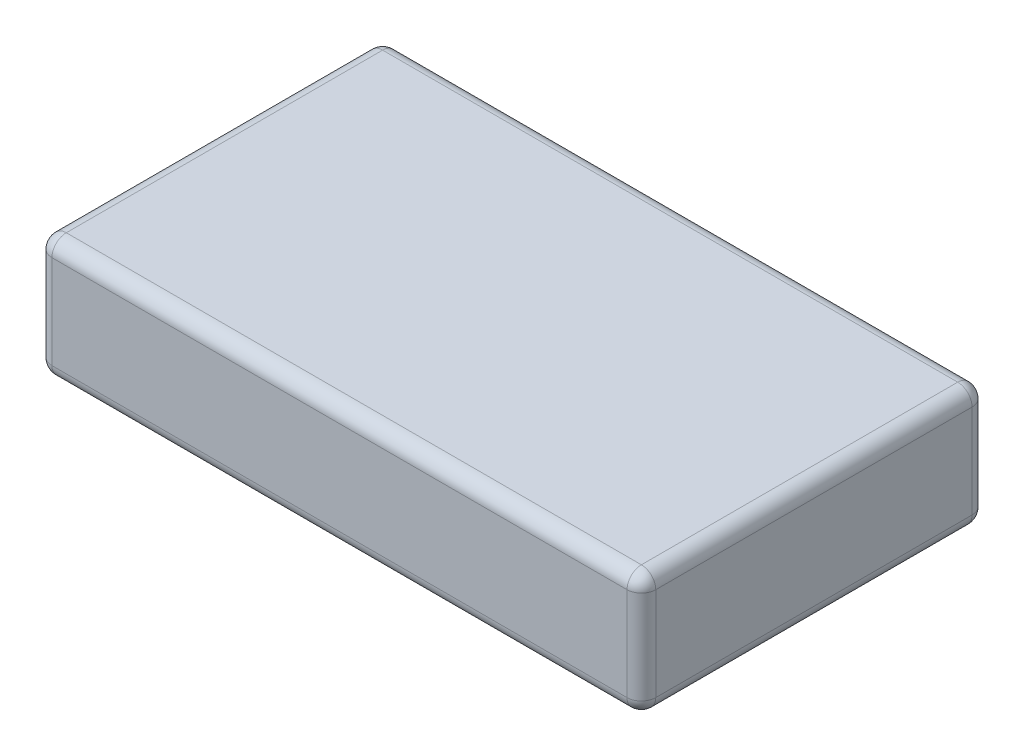
SolidWorks part; units mm, degrees
ref_plane "Front Plane" through (0, 0, 0) normal (0, 0, 1) x (1, 0, 0)
ref_plane "Top Plane" through (0, 0, 0) normal (0, 1, 0) x (1, 0, 0)
ref_plane "Right Plane" through (0, 0, 0) normal (1, 0, 0) x (0, 0, -1)
sketch "Sketch1" plane through (0, 0, 0) normal (0, 1, 0) x (1, 0, 0)
  line L1 (21, 12) -> (-21, 12)
  line L2 (21, 12) -> (21, -12)
  line L3 (21, -12) -> (-21, -12)
  line L4 (-21, 12) -> (-21, -12)
  line L5 (21, 12) -> (-21, -12) construction
  line L6 (21, -12) -> (-21, 12) construction
  point P0 (0, 0)
  dimension "D1" = 42
  dimension "D2" = 24
extrude "Boss-Extrude1" add sketch "Sketch1" along normal blind 8.5
fillet "Fillet1" radius 1 12 edges at (0, 0, 12) (-21, 0, 0) (-21, 4.25, 12) (-21, 4.25, -12) (0, 0, -12) (21, 4.25, -12) (21, 0, 0) (21, 4.25, 12) (-21, 8.5, 0) (21, 8.5, 0) (0, 8.5, -12) (0, 8.5, 12)
